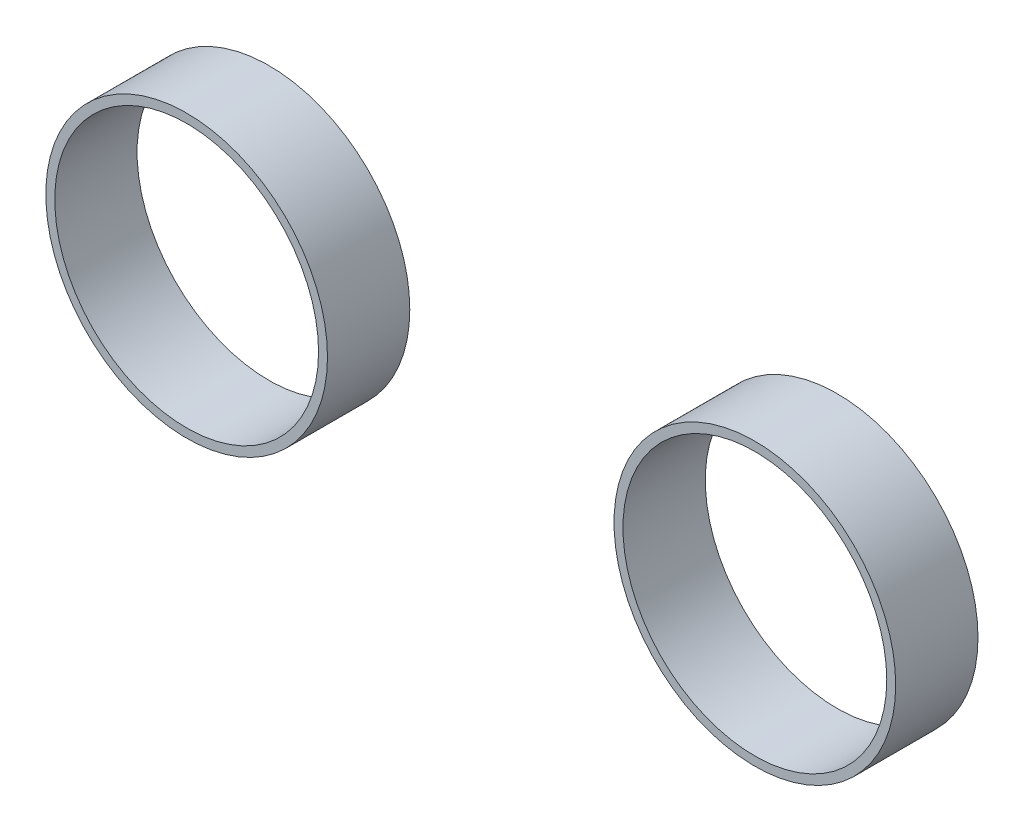
SolidWorks part; units mm, degrees
material "Velcro"
ref_plane "Front Plane" through (0, 0, 0) normal (0, 0, 1) x (1, 0, 0)
ref_plane "Top Plane" through (0, 0, 0) normal (0, 1, 0) x (1, 0, 0)
ref_plane "Right Plane" through (0, 0, 0) normal (1, 0, 0) x (0, 0, -1)
sketch "Sketch1" plane through (0, 0, 0) normal (0, 0, 1) x (1, 0, 0)
  circle A0 centre (1715.9805, -423.3823) radius 65 construction
  circle A1 centre (1715.9805, -423.3823) radius 69.4 construction
  circle A2 centre (1435.9805, -423.3823) radius 69.4 construction
  circle A3 centre (1435.9805, -423.3823) radius 65 construction
  circle A4 centre (1715.9805, -423.3823) radius 65
  circle A5 centre (1715.9805, -423.3823) radius 69.4
  circle A6 centre (1435.9805, -423.3823) radius 69.4
  circle A7 centre (1435.9805, -423.3823) radius 65
extrude "Boss-Extrude1" add sketch "Sketch1" along normal blind 40.56
